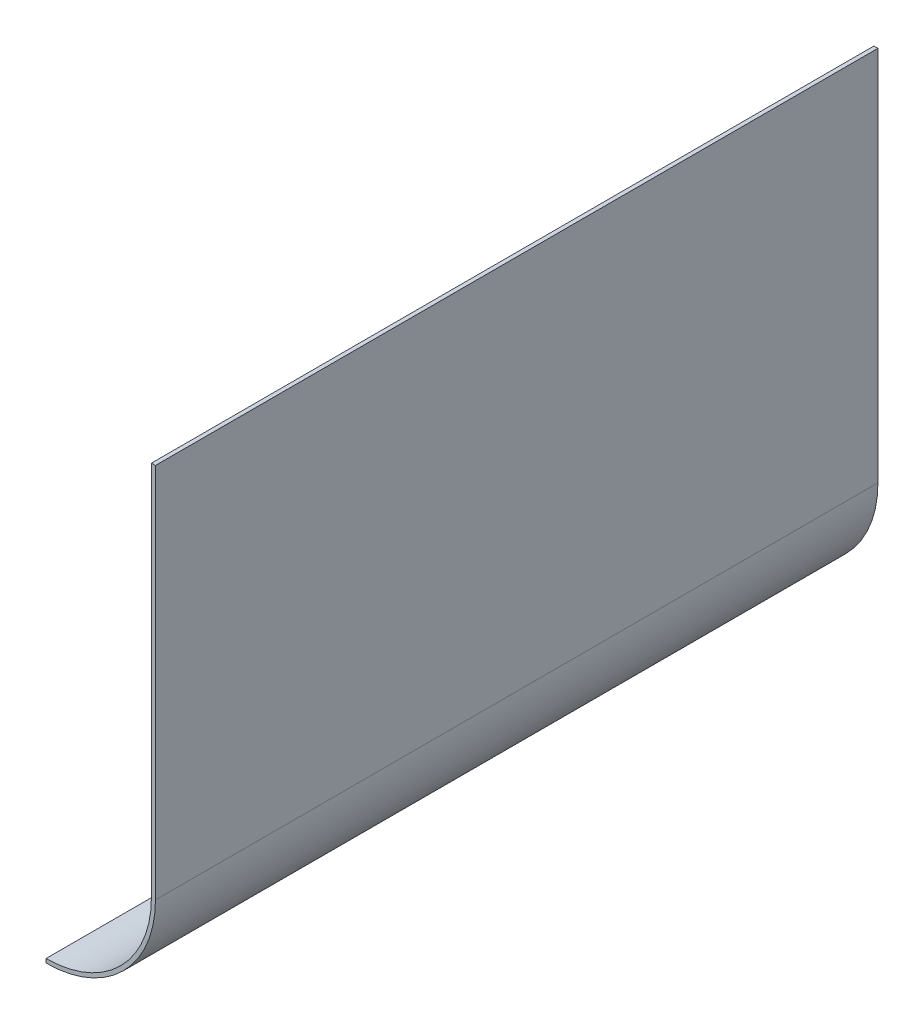
SolidWorks part; units mm, degrees
ref_plane "Front Plane" through (0, 0, 0) normal (0, 0, 1) x (1, 0, 0)
ref_plane "Top Plane" through (0, 0, 0) normal (0, 1, 0) x (1, 0, 0)
ref_plane "Right Plane" through (0, 0, 0) normal (1, 0, 0) x (0, 0, -1)
sketch "Sketch1" plane through (0, 0, 0) normal (0, 0, 1) x (1, 0, 0)
  line L0 (66.675, 238.125) -> (66.675, 0)
  line L1 (-89.835, -66.675) -> (0, -66.675) construction
  arc A0 (0, -66.675) -> (66.675, 0) centre (0, 0) ccw
  dimension "D1" = 66.675
  dimension "D2" = 304.8
extrude "Extrude-Thin1" add sketch "Sketch1" along normal blind 457.2 thin thin type one direction wall 2.54
